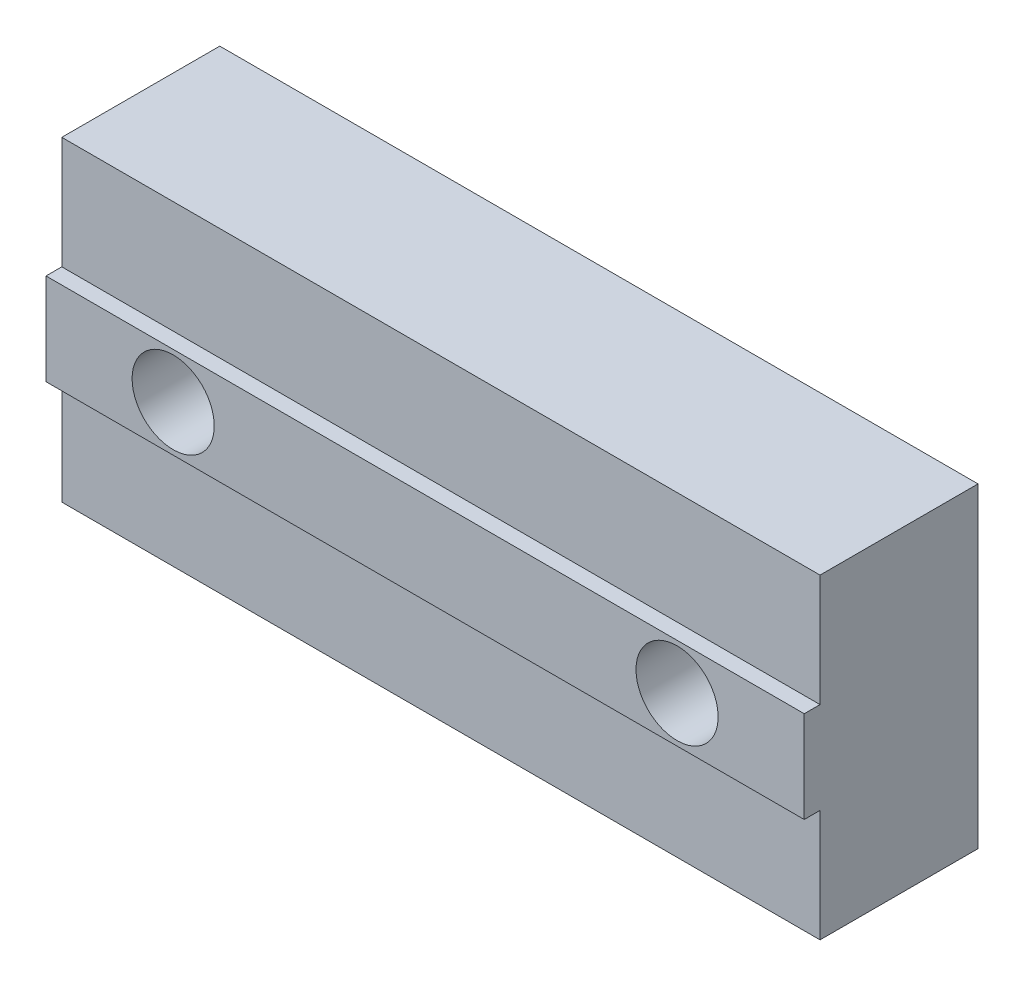
SolidWorks part; units mm, degrees
ref_plane "Front" through (0, 0, 0) normal (0, 0, 1) x (1, 0, 0)
ref_plane "Top" through (0, 0, 0) normal (0, 1, 0) x (1, 0, 0)
ref_plane "Right" through (0, 0, 0) normal (1, 0, 0) x (0, 0, -1)
sketch "Sketch1" plane through (0, 0, 0) normal (0, 0, 1) x (1, 0, 0)
  line L1 (-24, -10) -> (24, -10)
  line L2 (-24, -10) -> (-24, 10)
  line L3 (-24, 10) -> (24, 10)
  line L4 (24, -10) -> (24, 10)
  line L5 (-24, -10) -> (24, 10) construction
  line L6 (-24, 10) -> (24, -10) construction
  point P0 (0, 0)
  dimension "D1" = 20
  dimension "D2" = 48
extrude "Boss-Extrude1" add sketch "Sketch1" along normal blind 10
sketch "Sketch4" plane through (0, 0, 10) normal (0, 0, 1) x (1, 0, 0)
  line L0 (24, -10) -> (24, 10) construction
  line L1 (-24, -2.9) -> (24, -2.9)
  line L2 (-24, -2.9) -> (-24, 2.9)
  line L3 (-24, 2.9) -> (24, 2.9)
  line L4 (24, -2.9) -> (24, 2.9)
  line L5 (-24, -2.9) -> (24, 2.9) construction
  line L6 (-24, 2.9) -> (24, -2.9) construction
  point P0 (0, 0)
  dimension "D1" = 5.8
extrude "Boss-Extrude2" add sketch "Sketch4" along normal blind 1
sketch "Sketch2" plane through (0, 0, 0) normal (0, 0, 1) x (1, 0, 0)
  circle A0 centre (-15.95, 0) radius 2.6
  dimension "D1" = 5.2
  dimension "D2" = 15.95
extrude "Cut-Extrude1" cut sketch "Sketch2" along normal through all
mirror "Mirror1" about plane through (0, 0, 0) normal (1, 0, 0) of "Cut-Extrude1"
